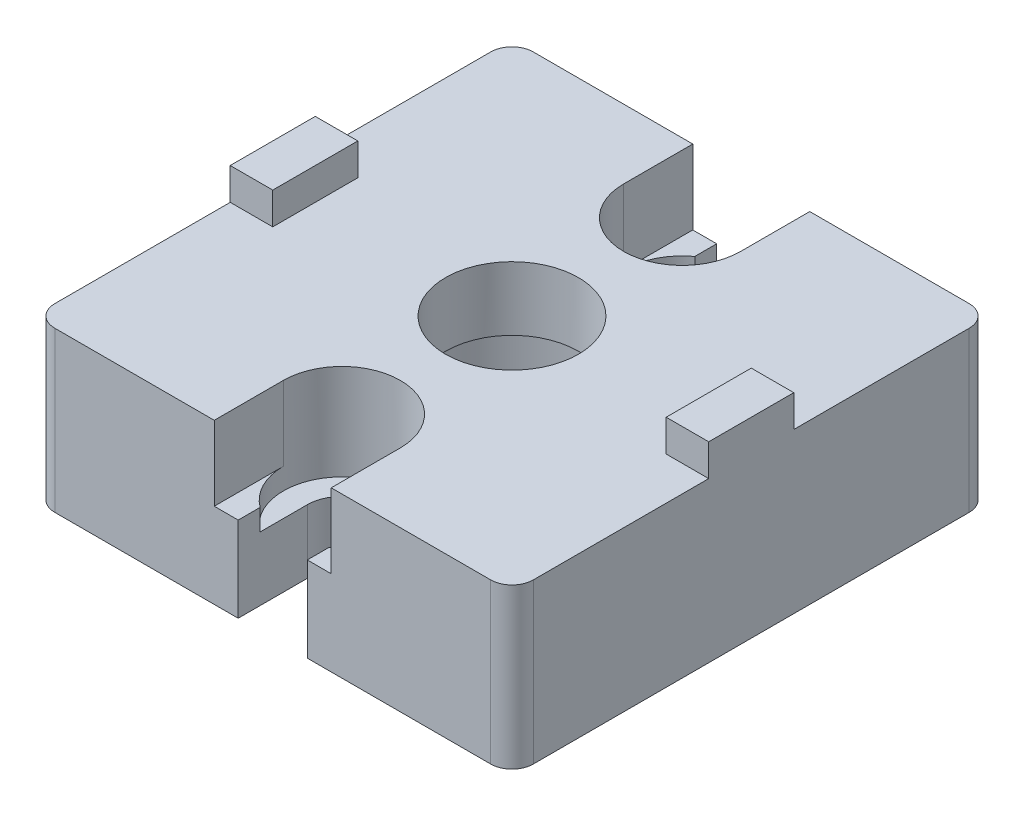
SolidWorks part; units mm, degrees
material "Алюминиевый сплав"
ref_plane "Спереди" through (0, 0, 0) normal (0, 0, 1) x (1, 0, 0)
ref_plane "Сверху" through (0, 0, 0) normal (0, 1, 0) x (1, 0, 0)
ref_plane "Справа" through (0, 0, 0) normal (1, 0, 0) x (0, 0, -1)
sketch "Эскиз1" plane through (0, 0, 0) normal (0, 1, 0) x (1, 0, 0)
  line L1 (22.5, 22.5) -> (-22.5, 22.5)
  line L2 (22.5, 22.5) -> (22.5, -22.5)
  line L3 (22.5, -22.5) -> (-22.5, -22.5)
  line L4 (-22.5, 22.5) -> (-22.5, -22.5)
  line L5 (22.5, 22.5) -> (-22.5, -22.5) construction
  line L6 (22.5, -22.5) -> (-22.5, 22.5) construction
  point P0 (0, 0)
  dimension "D1" = 45
extrude "Бобышка-Вытянуть1" add sketch "Эскиз1" along normal blind 15
sketch "Эскиз2" plane through (0, 15, 0) normal (0, 1, 0) x (1, 0, 0)
  line L0 (-22.5, 22.5) -> (-22.5, -22.5) construction
  line L1 (-18.5, -4) -> (-22.5, -4)
  line L2 (-18.5, -4) -> (-18.5, 4)
  line L3 (-18.5, 4) -> (-22.5, 4)
  line L4 (-22.5, -4) -> (-22.5, 4)
  line L5 (-18.5, -4) -> (-22.5, 4) construction
  line L6 (-18.5, 4) -> (-22.5, -4) construction
  line L7 (0, 0) -> (0, 6.185) construction
  line L8 (18.5, 4) -> (22.5, -4) construction
  line L9 (18.5, -4) -> (22.5, 4) construction
  line L10 (22.5, -4) -> (22.5, 4)
  line L11 (18.5, 4) -> (22.5, 4)
  line L12 (18.5, -4) -> (18.5, 4)
  line L13 (18.5, -4) -> (22.5, -4)
  point P0 (-20.5, 0)
  point P10 (0, 0)
  point P11 (-15, 1.8997)
  point P16 (20.5, 0)
  dimension "D1" = 4
  dimension "D2" = 8
extrude "Бобышка-Вытянуть2" add sketch "Эскиз2" along normal blind 3
sketch "Эскиз3" plane through (0, 15, 0) normal (0, 1, 0) x (1, 0, 0)
  line L0 (-3.25, -22.5) -> (-3.25, -16)
  line L1 (-22.5, -22.5) -> (22.5, -22.5) construction
  line L2 (3.25, -16) -> (3.25, -22.5)
  line L3 (3.25, -22.5) -> (-3.25, -22.5)
  line L4 (0, 0) -> (-17.3843, 0) construction
  line L5 (3.25, 16) -> (3.25, 22.5)
  line L6 (-3.25, 22.5) -> (-3.25, 16)
  line L7 (3.25, 22.5) -> (-3.25, 22.5)
  circle A0 centre (0, 0) radius 6.25
  arc A1 (-3.25, -16) -> (3.25, -16) centre (0, -16) cw
  arc A2 (-3.25, 16) -> (3.25, 16) centre (0, 16) ccw
  point P9 (0, 0)
  dimension "D1" = 12.5
  dimension "D2" = 3.25
  dimension "D3" = 32
extrude "Вырез-Вытянуть1" cut sketch "Эскиз3" against normal through all
sketch "Эскиз4" plane through (0, 0, 0) normal (0, -1, 0) x (1, 0, 0)
  circle A0 centre (0, 0) radius 10
  dimension "D1" = 20
extrude "Вырез-Вытянуть2" cut sketch "Эскиз4" against normal blind 9
sketch "Эскиз5" plane through (0, 15, 0) normal (0, 1, 0) x (1, 0, 0)
  line L0 (-5.5, -22.5) -> (-5.5, -16)
  line L1 (-22.5, -22.5) -> (-3.25, -22.5) construction
  line L2 (5.5, -16) -> (5.5, -22.5)
  line L3 (3.25, -22.5) -> (22.5, -22.5) construction
  line L4 (5.5, -22.5) -> (-5.5, -22.5)
  line L5 (0, 0) -> (-17.0309, 0) construction
  line L6 (5.5, 16) -> (5.5, 22.5)
  line L7 (-5.5, 22.5) -> (-5.5, 16)
  line L8 (5.5, 22.5) -> (-5.5, 22.5)
  arc A0 (-5.5, -16) -> (5.5, -16) centre (0, -16) cw
  arc A3 (-5.5, 16) -> (5.5, 16) centre (0, 16) ccw
  dimension "D1" = 5.5
extrude "Вырез-Вытянуть3" cut sketch "Эскиз5" against normal blind 7
sketch "Эскиз6" plane through (0, 8, 0) normal (0, 1, 0) x (1, 0, 0)
  circle A0 centre (0, -16) radius 5.5
  circle A1 centre (0, 16) radius 5.5
extrude "Вырез-Вытянуть4" cut sketch "Эскиз6" against normal blind 2
fillet "Скругление1" radius 2 4 edges at (-22.5, 7.5, -22.5) (22.5, 7.5, -22.5) (22.5, 7.5, 22.5) (-22.5, 7.5, 22.5)
